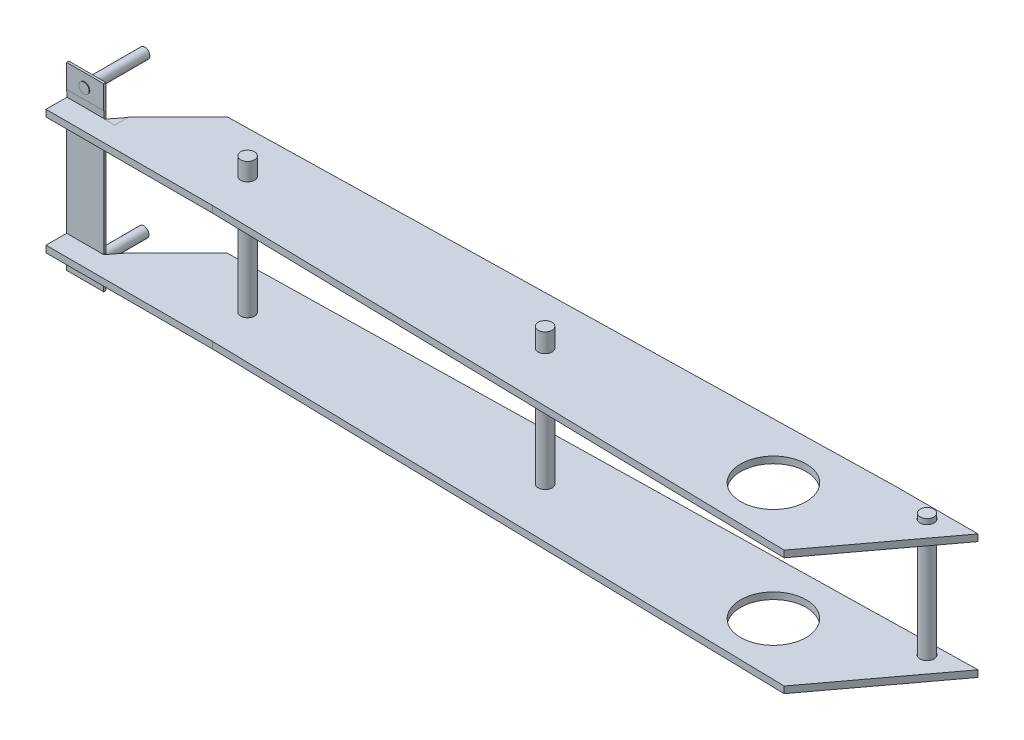
SolidWorks part; units mm, degrees
ref_plane "Alzado" through (0, 0, 0) normal (0, 0, 1) x (1, 0, 0)
ref_plane "Planta" through (0, 0, 0) normal (0, 1, 0) x (1, 0, 0)
ref_plane "Vista lateral" through (0, 0, 0) normal (1, 0, 0) x (0, 0, -1)
sketch "Croquis1" plane through (0, 0, 0) normal (0, 1, 0) x (1, 0, 0)
  line L0 (-101.794, -96.0985) -> (482.406, -96.0985) construction
  line L1 (-101.794, -70.6985) -> (-101.794, -121.4985)
  line L3 (482.406, -57.9985) -> (-101.794, -70.6985)
  line L4 (-101.794, -121.4985) -> (482.406, -134.1985)
  line L5 (482.406, -57.9985) -> (539.3167, -57.9985)
  line L6 (539.3167, -57.9985) -> (482.406, -134.1985)
  dimension "D1" = 584.2
  dimension "D2" = 50.8
  dimension "D3" = 76.2
extrude "Saliente-Extruir2" add sketch "Croquis1" along normal blind 4.572
sketch "Croquis4" plane through (0, 0, 0) normal (0, 1, 0) x (1, 0, 0)
  line L0 (-101.794, -121.4985) -> (-101.794, -96.0985)
  line L1 (-101.794, -70.6985) -> (-101.794, -121.4985) construction
  circle A0 centre (76.006, -96.0985) radius 4.7625
  circle A1 centre (280.2393, -96.0985) radius 4.7625
  dimension "D2" = 9.525
  dimension "D3" = 9.525
  dimension "D1" = 177.8
extrude "Cortar-Extruir2" cut sketch "Croquis4" against normal blind 98.552 and the other way blind 152.654 contours A1 | A0
sketch "Croquis5" plane through (0, 0, 0) normal (0, 1, 0) x (1, 0, 0)
  circle A0 centre (438.6942, -97.8201) radius 7.9375
  dimension "D1" = 15.875
extrude "Cortar-Extruir5" cut sketch "Croquis5" against normal blind 59.182 and the other way blind 47.498
sketch "Croquis6" plane through (0, 0, 0) normal (0, 1, 0) x (1, 0, 0)
  circle A0 centre (280.2393, -96.0985) radius 4.7625
  dimension "D1" = 9.525
extrude "Saliente-Extruir4" add sketch "Croquis6" against normal blind 94.488 and the other way blind 17.526
sketch "Croquis7" plane through (0, 0, 0) normal (0, 1, 0) x (1, 0, 0)
  circle A0 centre (76.006, -96.0985) radius 4.7625
  dimension "D1" = 9.525
extrude "Saliente-Extruir5" add sketch "Croquis7" against normal blind 97.536 and the other way blind 16.002
ref_plane "Plano32" through (0, -76.2, 0) normal (0, -1, 0) x (-1, 0, 0)
sketch "Croquis10" plane through (0, -76.2, 0) normal (0, -1, 0) x (-1, 0, 0)
  line L0 (-539.3167, -57.9985) -> (101.794, -70.6985)
  line L1 (101.794, -70.6985) -> (101.794, -121.4985)
  line L2 (101.794, -121.4985) -> (-482.406, -134.1985)
  line L3 (-482.406, -134.1985) -> (-539.3167, -57.9985)
  circle A0 centre (-438.6942, -97.8201) radius 7.9375
  dimension "D1" = 15.875
extrude "Saliente-Extruir6" add sketch "Croquis10" along normal blind 4.572
sketch "Croquis11" plane through (0, 0, 0) normal (0, 1, 0) x (1, 0, 0)
  circle A0 centre (438.6942, -97.8201) radius 22.479
  dimension "D1" = 44.958
extrude "Cortar-Extruir6" cut sketch "Croquis11" against normal blind 123.444 and the other way blind 97.282
sketch "Croquis12" plane through (0, 0, 0) normal (0, 1, 0) x (1, 0, 0)
  circle A0 centre (512.9769, -66.6294) radius 4.826
  dimension "D1" = 9.652
extrude "Cortar-Extruir7" cut sketch "Croquis12" against normal blind 187.96 and the other way blind 113.792
sketch "Croquis13" plane through (0, 4.572, 0) normal (0, 1, 0) x (1, 0, 0)
  circle A0 centre (512.9769, -66.6294) radius 4.6713
extrude "Saliente-Extruir8" add sketch "Croquis13" against normal blind 87.884 and the other way blind 3.556 separate body
sketch "Croquis14" plane through (0, 0, 0) normal (0, 1, 0) x (1, 0, 0)
  line L0 (33.8495, -67.7497) -> (0, -101.5993)
  line L1 (482.406, -57.9985) -> (-101.794, -70.6985) construction
  line L2 (0, -101.5993) -> (0, -123.7114)
  line L3 (-101.794, -121.4985) -> (482.406, -134.1985) construction
  line L4 (0, -123.7114) -> (-101.794, -121.4985)
  line L5 (-101.794, -121.4985) -> (-101.794, -70.6985)
  line L6 (-101.794, -70.6985) -> (33.8495, -67.7497)
extrude "Cortar-Extruir8" cut sketch "Croquis14" along normal blind 84.074 and the other way blind 142.748
sketch "Croquis15" plane through (0, 0, 0) normal (0, 1, 0) x (1, 0, 0)
  line L0 (81.3036, -125.4789) -> (-32.9964, -125.4789)
  line L1 (0, -123.7114) -> (482.406, -134.1985) construction
  line L2 (81.3036, -125.4789) -> (81.3036, -111.2924)
  line L3 (81.3036, -111.2924) -> (-32.9964, -111.2924)
  line L4 (-32.9964, -111.2924) -> (-32.9964, -125.4789)
  dimension "D1" = 114.3
extrude "Saliente-Extruir13" add sketch "Croquis15" against normal blind 86.106 and the other way blind 9.398
sketch "Croquis17" plane through (0, 0, 0) normal (0, 1, 0) x (1, 0, 0)
  line L0 (-7.54, -111.2924) -> (-32.9964, -111.2924)
  line L1 (81.3036, -111.2924) -> (-32.9964, -111.2924) construction
  line L3 (-32.9964, -111.2924) -> (-32.9964, -109.7788)
  line L4 (-32.9964, -109.7788) -> (-7.54, -109.7788)
  line L5 (-7.54, -109.7788) -> (-7.54, -111.2924)
extrude "Saliente-Extruir14" add sketch "Croquis17" against normal blind 98.298 and the other way blind 25.4
sketch "Croquis18" plane through (0, 0, 0) normal (1, 0, 0) x (0, 0, -1)
  line L0 (-125.4789, 0) -> (-111.7427, 0)
  line L1 (-125.4789, 9.398) -> (-125.4789, -86.106) construction
  line L2 (-111.7427, 0) -> (-111.7427, -76.2)
  line L3 (-41.91, -76.2) -> (41.91, -76.2) construction
  line L4 (-111.7427, -76.2) -> (-125.4789, -76.2)
  line L5 (-125.4789, -76.2) -> (-125.4789, 0)
extrude "Cortar-Extruir9" cut sketch "Croquis18" along normal blind 127.508
sketch "Croquis19" plane through (0, 0, 0) normal (1, 0, 0) x (0, 0, -1)
  line L0 (-125.4789, -1.7081) -> (-111.3111, -1.7081)
  line L2 (-125.4789, 9.398) -> (-125.4789, -86.106) construction
  line L3 (-111.3111, -1.7081) -> (-111.3111, -73.9951)
  line L5 (-111.3111, -73.9951) -> (-125.4789, -73.9951)
  line L6 (-125.4789, -73.9951) -> (-125.4789, -1.7081)
extrude "Cortar-Extruir12" cut sketch "Croquis19" against normal blind 127.508
sketch "Croquis20" plane through (0, 0, 111.7427) normal (0, 0, 1) x (1, 0, 0)
  line L0 (71.2435, -4.9445) -> (71.2435, -71.1848)
  line L1 (71.2435, 0) -> (71.2435, -76.2) construction
  line L2 (71.2435, -71.1848) -> (0, -71.1848)
  line L3 (0, -71.1848) -> (0, -4.9445)
  line L4 (0, -4.9445) -> (71.2435, -4.9445)
extrude "Cortar-Extruir13" cut sketch "Croquis20" along normal blind 289.306 and the other way blind 150.368
sketch "Croquis21" plane through (0, 0, 0) normal (0, 0, 1) x (1, 0, 0)
  line L0 (71.2435, -4.9445) -> (71.2435, -71.1848)
  line L1 (0, -71.1848) -> (71.2435, -71.1848) construction
  line L2 (71.2435, -71.1848) -> (71.2435, -4.9445) construction
  line L3 (0, -4.9445) -> (71.2435, -4.9445)
  line L5 (81.3036, 0) -> (81.3036, -76.2)
  line L6 (-41.91, -76.2) -> (41.91, -76.2) construction
  line L7 (81.3036, -76.2) -> (81.3036, 0) construction
  line L8 (81.3036, 0) -> (0, 0)
  line L9 (0, 0) -> (0, -4.9445)
  line L11 (71.2435, -71.1848) -> (81.3036, -76.2)
extrude "Cortar-Extruir14" cut sketch "Croquis21" along normal blind 662.432 and the other way blind 12.7
sketch "Croquis22" plane through (0, 0, 0) normal (0, 0, 1) x (1, 0, 0)
  line L0 (71.2435, -71.1848) -> (0, -71.1848)
  line L1 (0, -71.1848) -> (71.2435, -71.1848) construction
  line L2 (71.2435, -71.1848) -> (81.5446, -76.2)
  line L3 (-41.91, -76.2) -> (41.91, -76.2) construction
  line L4 (81.5446, -76.2) -> (0, -76.2)
  line L5 (0, -71.1848) -> (0, -76.2)
extrude "Cortar-Extruir15" cut sketch "Croquis22" along normal blind 397.51
sketch "Croquis23" plane through (0, 0, 0) normal (0, 1, 0) x (1, 0, 0)
  circle A0 centre (76.006, -96.0985) radius 4.7625
extrude "Saliente-Extruir15" add sketch "Croquis23" against normal blind 95.504 and the other way blind 16.764
sketch "Croquis24" plane through (0, 0, 0) normal (1, 0, 0) x (0, 0, -1)
  line L0 (-125.4789, 4.572) -> (-111.0954, 4.572)
  line L1 (-125.4789, 9.398) -> (-111.2924, 9.398)
  line L2 (-111.2924, 9.398) -> (-111.0954, 4.572)
  line L3 (-125.4789, 9.398) -> (-125.4789, 4.572)
extrude "Cortar-Extruir17" cut sketch "Croquis24" along normal blind 83.566 and the other way blind 37.846
sketch "Croquis25" plane through (0, 0, 0) normal (1, 0, 0) x (0, 0, -1)
  line L0 (-125.4789, -86.106) -> (-125.4789, -80.772)
  line L1 (-125.4789, -80.772) -> (-111.2924, -80.772)
  line L2 (-111.2924, -80.772) -> (-111.2924, -86.106)
  line L3 (-111.2924, -86.106) -> (-125.4789, -86.106)
extrude "Cortar-Extruir18" cut sketch "Croquis25" along normal blind 88.138 and the other way blind 41.402
sketch "Croquis26" plane through (0, 0, 0) normal (1, 0, 0) x (0, 0, -1)
  line L0 (-61.9581, -37.592) -> (-143.8943, -37.592)
  line L1 (-61.9581, -83.312) -> (-61.9581, 8.128) construction
  line L2 (-125.4789, -1.7081) -> (-125.4789, 0)
  line L3 (-125.4789, 4.572) -> (-125.4789, -1.7081) construction
  line L4 (-125.4789, 0) -> (-111.4596, 0)
  line L5 (-111.4596, 0) -> (-111.4596, -1.7081)
  line L6 (-111.3111, -1.7081) -> (-125.4789, -1.7081) construction
  line L7 (-111.4596, -1.7081) -> (-125.4789, -1.7081)
extrude "Cortar-Extruir19" cut sketch "Croquis26" along normal blind 41.402 and the other way blind 67.31 contours L4 L5 L7 L2
sketch "Croquis27" plane through (0, 0, 0) normal (1, 0, 0) x (0, 0, -1)
  line L0 (-111.3111, -73.9951) -> (-125.4789, -73.9951)
  line L1 (-125.4789, -73.9951) -> (-125.4789, -76.2)
  line L2 (-125.4789, -76.2) -> (-111.3111, -76.2)
  line L3 (-41.91, -76.2) -> (41.91, -76.2) construction
  line L4 (-111.3111, -76.2) -> (-111.3111, -73.9951)
extrude "Cortar-Extruir20" cut sketch "Croquis27" along normal blind 48.26 and the other way blind 71.628
sketch "Croquis28" plane through (0, 0, 0) normal (0, 0, 1) x (1, 0, 0)
  line L0 (0, -1.7081) -> (0, -76.2)
  line L1 (-41.91, -76.2) -> (41.91, -76.2) construction
  line L2 (0, -76.2) -> (0, -1.7081) construction
  line L3 (0, -76.2) -> (-7.6145, -76.2)
  line L4 (-7.6145, -76.2) -> (-7.6145, -1.7081)
  line L5 (-32.9964, -1.7081) -> (0, -1.7081) construction
  line L6 (-7.6145, -1.7081) -> (0, -1.7081)
extrude "Cortar-Extruir21" cut sketch "Croquis28" along normal blind 254
sketch "Croquis29" plane through (0, 0, 0) normal (0, 0, 1) x (1, 0, 0)
  line L0 (-7.4988, 0) -> (-7.4988, -1.7081)
  line L1 (-32.9964, 0) -> (0, 0) construction
  line L2 (-32.9964, -1.7081) -> (0, -1.7081) construction
  line L3 (-7.4988, -1.7081) -> (0, -1.7081)
  line L4 (0, -1.7081) -> (0, 0)
  line L5 (0, 0) -> (-7.4988, 0)
extrude "Cortar-Extruir22" cut sketch "Croquis29" along normal blind 340.106
sketch "Croquis30" plane through (0, 0, 0) normal (0, 1, 0) x (1, 0, 0)
  line L0 (-7.54, -111.2924) -> (0, -101.5993)
  line L1 (0, -101.5993) -> (0, -111.2924)
  line L2 (0, -111.2924) -> (-7.54, -111.2924)
extrude "Saliente-Extruir19" add sketch "Croquis30" against normal blind 80.264 and the other way blind 4.318
sketch "Croquis32" plane through (0, 0, 0) normal (0, 0, 1) x (1, 0, 0)
  line L0 (-7.4764, -76.2) -> (0, -76.2)
  line L1 (-41.91, -76.2) -> (41.91, -76.2) construction
  line L2 (0, 0) -> (0, -76.2) construction
  line L3 (0, -76.2) -> (0, 0)
  line L4 (0, 0) -> (-7.4764, 0)
  line L5 (81.3036, 0) -> (-32.9964, 0) construction
  line L6 (-7.4764, 0) -> (-7.4764, -76.2)
extrude "Cortar-Extruir24" cut sketch "Croquis32" along normal blind 209.042
sketch "Croquis33" plane through (0, 0, 0) normal (0, 0, 1) x (1, 0, 0)
  circle A0 centre (-20.6465, 16.5327) radius 3.5287
extrude "Saliente-Extruir20" add sketch "Croquis33" along normal blind 111.76
sketch "Croquis34" plane through (0, 0, 0) normal (0, 1, 0) x (1, 0, 0)
  line L0 (-24.1752, -70.0261) -> (-17.1178, -70.0261)
  line L1 (-24.1752, 0) -> (-24.1752, -109.7788) construction
  line L2 (-17.1178, -109.7788) -> (-17.1178, 0) construction
  line L3 (-24.1752, 0) -> (-17.1178, 0)
  line L4 (-17.1178, 0) -> (-24.1752, 0) construction
  line L5 (-17.1178, 0) -> (-17.1178, -70.0261)
  line L6 (-24.1752, 0) -> (-24.1752, -70.0261)
extrude "Cortar-Extruir25" cut sketch "Croquis34" along normal blind 200.406
sketch "Croquis35" plane through (0, 0, 0) normal (0, 0, 1) x (1, 0, 0)
  circle A0 centre (-20.6465, -89.4391) radius 3.556
  dimension "D1" = 7.112
extrude "Saliente-Extruir21" add sketch "Croquis35" along normal blind 110.998 and the other way blind 5.08
sketch "Croquis36" plane through (-32.9964, 0, 0) normal (-1, 0, 0) x (0, 0, 1)
  line L0 (70.6803, -85.8831) -> (70.6803, -92.9951)
  line L1 (109.7788, -85.8831) -> (-5.08, -85.8831) construction
  line L2 (-5.08, -92.9951) -> (109.7788, -92.9951) construction
  line L3 (70.6803, -92.9951) -> (-5.08, -92.9951)
  line L4 (-5.08, -85.8831) -> (-5.08, -92.9951) construction
  line L5 (-5.08, -92.9951) -> (-5.08, -85.8831)
  line L6 (-5.08, -85.8831) -> (70.6803, -85.8831)
extrude "Cortar-Extruir26" cut sketch "Croquis36" along normal blind 55.626 and the other way blind 67.818
